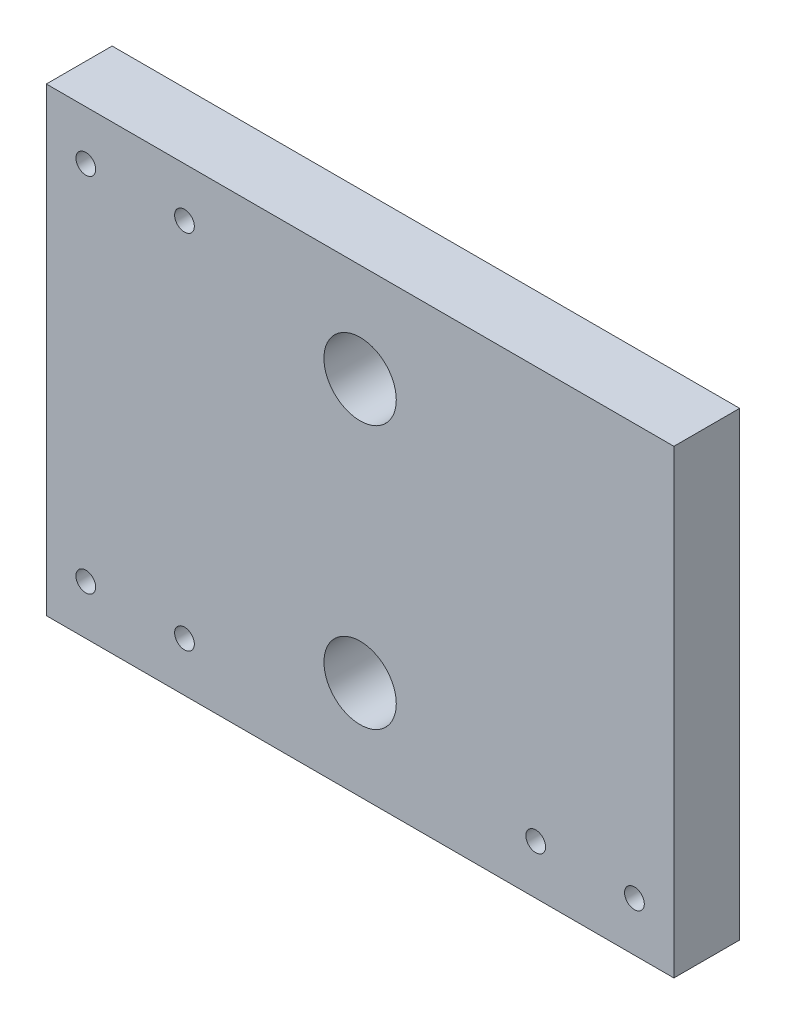
SolidWorks part; units mm, degrees
ref_plane "Front Plane" through (0, 0, 0) normal (0, 0, 1) x (1, 0, 0)
ref_plane "Top Plane" through (0, 0, 0) normal (0, 1, 0) x (1, 0, 0)
ref_plane "Right Plane" through (0, 0, 0) normal (1, 0, 0) x (0, 0, -1)
sketch "Sketch1" plane through (0, 0, 0) normal (0, 0, 1) x (1, 0, 0)
  line L0 (0, 0) -> (0, 40) construction
  line L2 (12.5, -15) -> (-12.5, -15)
  line L3 (12.5, -15) -> (12.5, 55)
  line L4 (12.5, 55) -> (-12.5, 55)
  line L5 (-12.5, -15) -> (-12.5, 55)
  line L6 (12.5, -15) -> (-12.5, 55) construction
  line L7 (12.5, 55) -> (-12.5, -15) construction
  circle A0 centre (0, 40) radius 7.9375
  circle A1 centre (0, 0) radius 7.9375
  point P5 (0, 20)
  dimension "D2" = 15.875
  dimension "D1" = 40
  dimension "D3" = 70
  dimension "D4" = 25
extrude "Boss-Extrude1" add sketch "Sketch1" along normal blind 10
sketch "Sketch2" plane through (0, 0, 10) normal (0, 0, 1) x (1, 0, 0)
  line L0 (12.5, 55) -> (-12.5, 55) construction
  line L1 (-47.7, 55) -> (-8.2, 55)
  line L3 (-47.7, -15) -> (-8.2, -15)
  line L4 (-8.2, 55) -> (-8.2, 35.0594)
  line L5 (-8.2, 35.0594) -> (-8.2, 32.231)
  line L6 (8.2, 35.0594) -> (8.2, 32.231)
  line L7 (-12.5, -15) -> (12.5, -15) construction
  line L8 (-8.2, 32.231) -> (-8.2, 4.0594)
  line L9 (-8.2, 1.231) -> (-8.2, 4.0594)
  line L16 (8.2, 1.231) -> (8.2, 4.0594)
  line L24 (8.2, 55) -> (8.2, 35.0594)
  line L25 (47.7, -15) -> (8.2, -15)
  line L27 (47.7, 55) -> (8.2, 55)
  line L28 (-47.7, 55) -> (-47.7, -15)
  line L29 (47.7, 55) -> (47.7, -15)
  line L31 (-8.2, 1.231) -> (-8.2, -15)
  line L32 (8.2, 1.231) -> (8.2, -15)
  line L33 (8.2, 32.231) -> (8.2, 4.0594)
extrude "Boss-Extrude2" add sketch "Sketch2" against normal up to surface (10 mm away) up to face at (0, 20, 0)
sketch "Sketch3" plane through (0, 0, 10) normal (0, 0, 1) x (1, 0, 0)
  circle A0 centre (0, 40) radius 5.5
  circle A1 centre (0, 0) radius 5.5
  circle A2 centre (0, 40) radius 7.9375 construction
  circle A3 centre (0, 40) radius 7.9375
  circle A4 centre (0, 0) radius 7.9375 construction
  circle A5 centre (0, 0) radius 7.9375
  dimension "D1" = 11
extrude "Boss-Extrude3" add sketch "Sketch3" against normal blind 8
sketch "Sketch4" plane through (0, 0, 0) normal (0, 0, -1) x (-1, 0, 0)
  circle A0 centre (26.7, 47.5) radius 1.5 construction
  circle A1 centre (41.7, 47.5) radius 1.5 construction
  circle A2 centre (-41.7, -7.5) radius 1.5 construction
  circle A3 centre (-26.7, -7.5) radius 1.5 construction
  circle A4 centre (41.7, -7.5) radius 1.5 construction
  circle A5 centre (26.7, -7.5) radius 1.5 construction
  circle A6 centre (26.7, 47.5) radius 1.5
  circle A7 centre (41.7, 47.5) radius 1.5
  circle A8 centre (-41.7, -7.5) radius 1.5
  circle A9 centre (-26.7, -7.5) radius 1.5
  circle A10 centre (41.7, -7.5) radius 1.5
  circle A11 centre (26.7, -7.5) radius 1.5
extrude "Cut-Extrude1" cut sketch "Sketch4" against normal through all
